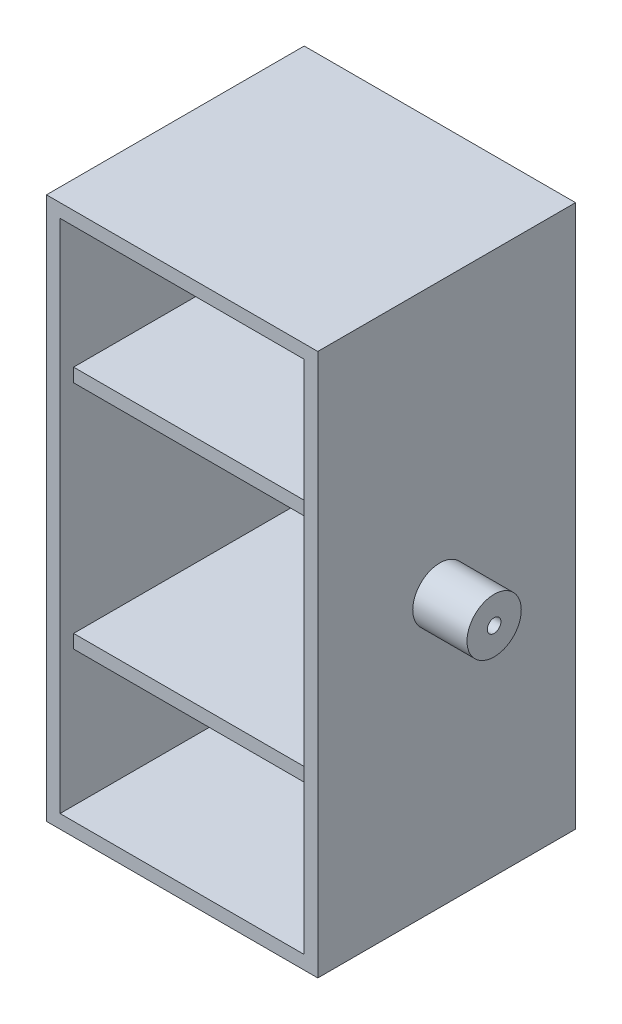
SolidWorks part; units mm, degrees
ref_plane "Front Plane" through (0, 0, 0) normal (0, 0, 1) x (1, 0, 0)
ref_plane "Top Plane" through (0, 0, 0) normal (0, 1, 0) x (1, 0, 0)
ref_plane "Right Plane" through (0, 0, 0) normal (1, 0, 0) x (0, 0, -1)
sketch "Sketch2" plane through (0, 0, 0) normal (0, 1, 0) x (1, 0, 0)
  line L1 (0, 0) -> (100, 0)
  line L2 (0, 0) -> (0, -100)
  line L3 (0, -100) -> (100, -100)
  line L4 (100, 0) -> (100, -100)
  dimension "D1" = 100
  dimension "D2" = 100
extrude "Boss-Extrude1" add sketch "Sketch2" along normal blind 200
shell "Shell3" thickness 5
sketch "Sketch3" plane through (0, 0, 5) normal (0, 0, 1) x (1, 0, 0)
  line L0 (5, 195) -> (5, 5) construction
  line L1 (5, 55) -> (95, 55)
  line L2 (5, 55) -> (5, 60)
  line L3 (5, 60) -> (95, 60)
  line L4 (95, 55) -> (95, 60)
  line L5 (95, 195) -> (95, 5) construction
  line L6 (95, 5) -> (5, 5) construction
  line L7 (95, 195) -> (5, 195) construction
  line L8 (5, 145) -> (95, 145)
  line L9 (5, 145) -> (5, 140)
  line L10 (5, 140) -> (95, 140)
  line L11 (95, 145) -> (95, 140)
  dimension "D1" = 5
  dimension "D2" = 50
  dimension "D3" = 5
  dimension "D4" = 50
extrude "Boss-Extrude2" add sketch "Sketch3" along normal blind 85
sketch "Sketch4" plane through (100, 0, 0) normal (1, 0, 0) x (0, 0, -1)
  line L0 (-1000, 100) -> (49000, 100) construction
  line L1 (0, 200) -> (0, 0) construction
  line L2 (-50, 200) -> (-50, 100) construction
  line L3 (-100, 200) -> (0, 200) construction
  circle A0 centre (-50, 100) radius 10
  circle A1 centre (-50, 100) radius 2.5
  point P5 (0, 100)
  dimension "D1" = 20
  dimension "D2" = 5
extrude "Boss-Extrude3" add sketch "Sketch4" along normal blind 20
sketch "Sketch5" plane through (0, 0, 0) normal (-1, 0, 0) x (0, 0, 1)
  line L0 (0, 100) -> (100, 100) construction
  line L1 (0, 200) -> (0, 0) construction
  line L2 (100, 200) -> (100, 0) construction
  line L3 (50, 200) -> (50, 100) construction
  line L4 (0, 200) -> (100, 200) construction
  circle A0 centre (50, 100) radius 10
  circle A1 centre (50, 100) radius 2.5
  dimension "D1" = 20
  dimension "D2" = 5
extrude "Boss-Extrude4" add sketch "Sketch5" along normal blind 20
sketch "Sketch7" plane through (0, 0, 100) normal (0, 0, 1) x (1, 0, 0)
  line L0 (0, 200) -> (100, 200) construction
  line L1 (0, 200) -> (95, 200)
  line L2 (0, 200) -> (0, 195)
  line L3 (0, 195) -> (95, 195)
  line L4 (95, 200) -> (95, 195)
  line L6 (95, 200) -> (100, 200)
  line L7 (95, 200) -> (95, 0)
  line L8 (95, 0) -> (100, 0)
  line L9 (100, 200) -> (100, 0)
  line L10 (95, 0) -> (5, 0)
  line L11 (95, 0) -> (95, 5)
  line L12 (95, 5) -> (5, 5)
  line L13 (5, 0) -> (5, 5)
  line L14 (5, 0) -> (0, 0)
  line L15 (5, 0) -> (5, 195)
  line L16 (5, 195) -> (0, 195)
  line L17 (0, 0) -> (0, 195)
  line M18 (0, 0) -> (100, 0)
  line M19 (100, 0) -> (100, 200)
  line M20 (100, 200) -> (0, 200)
  line M21 (0, 200) -> (0, 0)
  line M22 (95, 5) -> (5, 5)
  line M23 (5, 5) -> (5, 195)
  line M24 (5, 195) -> (95, 195)
  line M25 (95, 195) -> (95, 5)
extrude "Cut-Extrude1" cut sketch "Sketch7" against normal blind 5 contours L4 L3 M20 M21 M24 | L7 L4 M25 M18 M19 M20 | L13 L3 M18 M23 M21 | L13 L7 M18 M22
